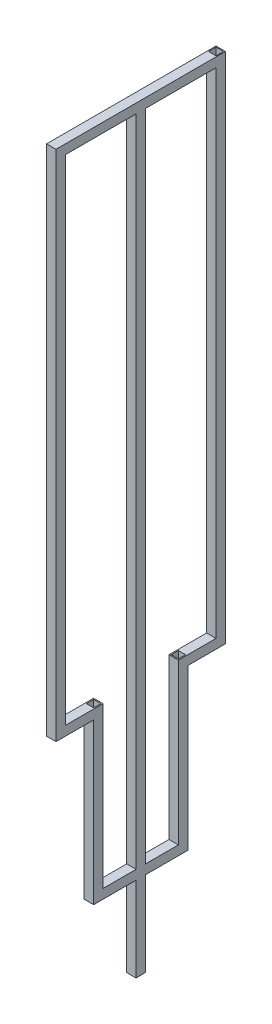
SolidWorks part; units mm, degrees
ref_plane "Front" through (0, 0, 0) normal (0, 0, 1) x (1, 0, 0)
ref_plane "Top" through (0, 0, 0) normal (0, 1, 0) x (1, 0, 0)
ref_plane "Right" through (0, 0, 0) normal (1, 0, 0) x (0, 0, -1)
sketch "Sketch1" plane through (0, 0, 0) normal (0, 1, 0) x (1, 0, 0)
  line L1 (-1, -1) -> (1, -1)
  line L2 (-1, -1) -> (-1, 1)
  line L3 (-1, 1) -> (1, 1)
  line L4 (1, -1) -> (1, 1)
  line L5 (-1, -1) -> (1, 1) construction
  line L6 (-1, 1) -> (1, -1) construction
  line L7 (-0.8, 0.8) -> (0.8, 0.8)
  line L8 (-0.8, 0.8) -> (-0.8, -0.8)
  line L9 (-0.8, -0.8) -> (0.8, -0.8)
  line L10 (0.8, 0.8) -> (0.8, -0.8)
  line L11 (-0.8, 0.8) -> (0.8, -0.8) construction
  line L12 (-0.8, -0.8) -> (0.8, 0.8) construction
  point P0 (0, 0)
  point P6 (0, 0)
  dimension "D1" = 2
  dimension "D2" = 2
  dimension "D3" = 0.2
  dimension "D4" = 0.2
extrude "Boss-Extrude1" add sketch "Sketch1" along normal blind 109
sketch "Sketch2" plane through (0, 0, 1) normal (0, 0, 1) x (1, 0, 0)
  line L1 (-1, 107) -> (1, 107)
  line L2 (-1, 107) -> (-1, 109)
  line L3 (-1, 109) -> (1, 109)
  line L4 (1, 107) -> (1, 109)
  line L5 (-1, 107) -> (1, 109) construction
  line L6 (-1, 109) -> (1, 107) construction
  line L7 (-0.8, 108.8) -> (0.8, 108.8)
  line L8 (-0.8, 108.8) -> (-0.8, 107.2)
  line L9 (-0.8, 107.2) -> (0.8, 107.2)
  line L10 (0.8, 108.8) -> (0.8, 107.2)
  line L11 (-0.8, 108.8) -> (0.8, 107.2) construction
  line L12 (-0.8, 107.2) -> (0.8, 108.8) construction
  point P0 (0, 108)
  point P6 (0, 108)
  dimension "D1" = 0.2
  dimension "D2" = 0.2
  dimension "D3" = 2
  dimension "D4" = 2
extrude "Boss-Extrude2" add sketch "Sketch2" along normal blind 34
ref_plane "Plane1" through (0, 0, 17) normal (0, 0, 1) x (1, 0, 0)
mirror "Mirror1" about plane through (0, 0, 17) normal (0, 0, 1) of "Boss-Extrude1"
sketch "Sketch3" plane through (0, 0, 1) normal (0, 0, 1) x (1, 0, 0)
  line L1 (1, 2) -> (-1, 2)
  line L2 (1, 2) -> (1, 0)
  line L3 (1, 0) -> (-1, 0)
  line L4 (-1, 2) -> (-1, 0)
  line L5 (1, 2) -> (-1, 0) construction
  line L6 (1, 0) -> (-1, 2) construction
  line L7 (0.8, 1.8) -> (-0.8, 1.8)
  line L8 (0.8, 1.8) -> (0.8, 0.2)
  line L9 (0.8, 0.2) -> (-0.8, 0.2)
  line L10 (-0.8, 1.8) -> (-0.8, 0.2)
  line L11 (0.8, 1.8) -> (-0.8, 0.2) construction
  line L12 (0.8, 0.2) -> (-0.8, 1.8) construction
  point P0 (0, 1)
  point P6 (0, 1)
  dimension "D1" = 2
  dimension "D2" = 0.2
extrude "Boss-Extrude3" add sketch "Sketch3" along normal blind 6
sketch "Sketch7" plane through (0, 2, 0) normal (0, 1, 0) x (1, 0, 0)
  line L1 (-1, -9) -> (1, -9)
  line L2 (-1, -9) -> (-1, -7)
  line L3 (-1, -7) -> (1, -7)
  line L4 (1, -9) -> (1, -7)
  line L5 (-1, -9) -> (1, -7) construction
  line L6 (-1, -7) -> (1, -9) construction
  line L7 (-0.77, -7.23) -> (0.77, -7.23)
  line L8 (-0.77, -7.23) -> (-0.77, -8.77)
  line L9 (-0.77, -8.77) -> (0.77, -8.77)
  line L10 (0.77, -7.23) -> (0.77, -8.77)
  line L11 (-0.77, -7.23) -> (0.77, -8.77) construction
  line L12 (-0.77, -8.77) -> (0.77, -7.23) construction
  point P0 (0, -8)
  point P6 (0, -8)
  dimension "D1" = 2
  dimension "D2" = 0.23
extrude "Boss-Extrude4" add sketch "Sketch7" against normal blind 36
mirror "Mirror2" about plane through (0, 0, 17) normal (0, 0, 1) of "Boss-Extrude4", "Boss-Extrude3"
sketch "Sketch8" plane through (0, 0, 25) normal (0, 0, -1) x (-1, 0, 0)
  line L1 (-1, -32) -> (1, -32)
  line L2 (-1, -32) -> (-1, -34)
  line L3 (-1, -34) -> (1, -34)
  line L4 (1, -32) -> (1, -34)
  line L5 (-1, -32) -> (1, -34) construction
  line L6 (-1, -34) -> (1, -32) construction
  line L7 (-0.8, -32.2) -> (0.8, -32.2)
  line L8 (-0.8, -32.2) -> (-0.8, -33.8)
  line L9 (-0.8, -33.8) -> (0.8, -33.8)
  line L10 (0.8, -32.2) -> (0.8, -33.8)
  line L11 (-0.8, -32.2) -> (0.8, -33.8) construction
  line L12 (-0.8, -33.8) -> (0.8, -32.2) construction
  point P0 (0, -33)
  point P6 (0, -33)
  dimension "D1" = 2
  dimension "D2" = 0.2
extrude "Boss-Extrude5" add sketch "Sketch8" along normal up to next
scale "Scale2" scale about origin uniform scaling yes scale factor 10
sketch "Sketch9" plane through (0, 1070, 0) normal (0, -1, 0) x (1, 0, 0)
  line L0 (-10, 330) -> (-10, 10) construction
  line L1 (10, 179.7381) -> (-10, 179.7381)
  line L2 (10, 179.7381) -> (10, 159.7381)
  line L3 (10, 159.7381) -> (-10, 159.7381)
  line L4 (-10, 179.7381) -> (-10, 159.7381)
  line L5 (10, 179.7381) -> (-10, 159.7381) construction
  line L6 (10, 159.7381) -> (-10, 179.7381) construction
  line L8 (8, 177.7381) -> (-8, 177.7381)
  line L9 (8, 177.7381) -> (8, 161.7381)
  line L10 (8, 161.7381) -> (-8, 161.7381)
  line L11 (-8, 177.7381) -> (-8, 161.7381)
  line L12 (8, 177.7381) -> (-8, 161.7381) construction
  line L13 (8, 161.7381) -> (-8, 177.7381) construction
  point P0 (0, 169.7381)
  point P7 (0, 169.7381)
  dimension "D1" = 20
  dimension "D2" = 2
extrude "Boss-Extrude6" add sketch "Sketch9" along normal up to next
sketch "Sketch10" plane through (0, -340, 0) normal (0, -1, 0) x (1, 0, 0)
  line L0 (10, 270) -> (10, 70) construction
  line L1 (-10, 180) -> (10, 180)
  line L2 (-10, 180) -> (-10, 160)
  line L3 (-10, 160) -> (10, 160)
  line L4 (10, 180) -> (10, 160)
  line L5 (-10, 180) -> (10, 160) construction
  line L6 (-10, 160) -> (10, 180) construction
  line L8 (-8, 178) -> (8, 178)
  line L9 (-8, 178) -> (-8, 162)
  line L10 (-8, 162) -> (8, 162)
  line L11 (8, 178) -> (8, 162)
  line L12 (-8, 178) -> (8, 162) construction
  line L13 (-8, 162) -> (8, 178) construction
  point P0 (0, 170)
  point P9 (10, 170)
  point P10 (10, 170)
  point P11 (0, 170)
  dimension "D1" = 20
  dimension "D2" = 2
extrude "Boss-Extrude7" add sketch "Sketch10" along normal blind 179.85
